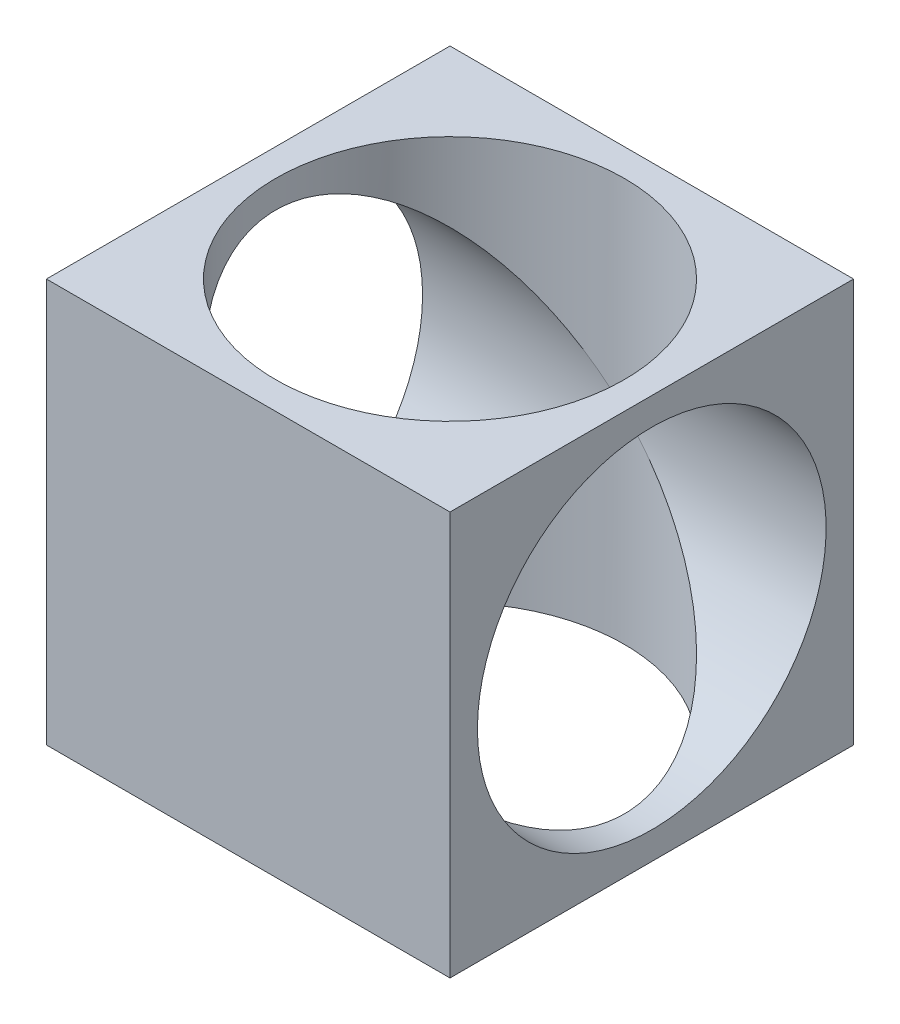
SolidWorks part; units mm, degrees
ref_plane "Front Plane" through (0, 0, 0) normal (0, 0, 1) x (1, 0, 0)
ref_plane "Top Plane" through (0, 0, 0) normal (0, 1, 0) x (1, 0, 0)
ref_plane "Right Plane" through (0, 0, 0) normal (1, 0, 0) x (0, 0, -1)
sketch "Sketch2" plane through (0, 0, 0) normal (0, 1, 0) x (1, 0, 0)
  line L1 (-15.875, -15.875) -> (15.875, -15.875)
  line L2 (-15.875, -15.875) -> (-15.875, 15.875)
  line L3 (-15.875, 15.875) -> (15.875, 15.875)
  line L4 (15.875, -15.875) -> (15.875, 15.875)
  line L5 (-15.875, -15.875) -> (15.875, 15.875) construction
  line L6 (-15.875, 15.875) -> (15.875, -15.875) construction
  point P0 (0, 0)
  dimension "D1" = 31.75
  dimension "D2" = 31.75
extrude "Boss-Extrude1" add sketch "Sketch2" along normal blind 31.75
sketch "Sketch3" plane through (0, 31.75, 0) normal (0, 1, 0) x (1, 0, 0)
  circle A0 centre (0, 0) radius 13.716
  dimension "D1" = 27.432
extrude "Cut-Extrude1" cut sketch "Sketch3" against normal through all both and the other way through all
sketch "Sketch4" plane through (-15.875, 0, 0) normal (-1, 0, 0) x (0, 0, 1)
  line L0 (-15.875, 31.75) -> (-15.875, 0) construction
  circle A0 centre (0, 15.875) radius 13.716
  point P5 (-15.875, 15.875)
  dimension "D1" = 27.432
extrude "Cut-Extrude2" cut sketch "Sketch4" against normal through all both and the other way through all
